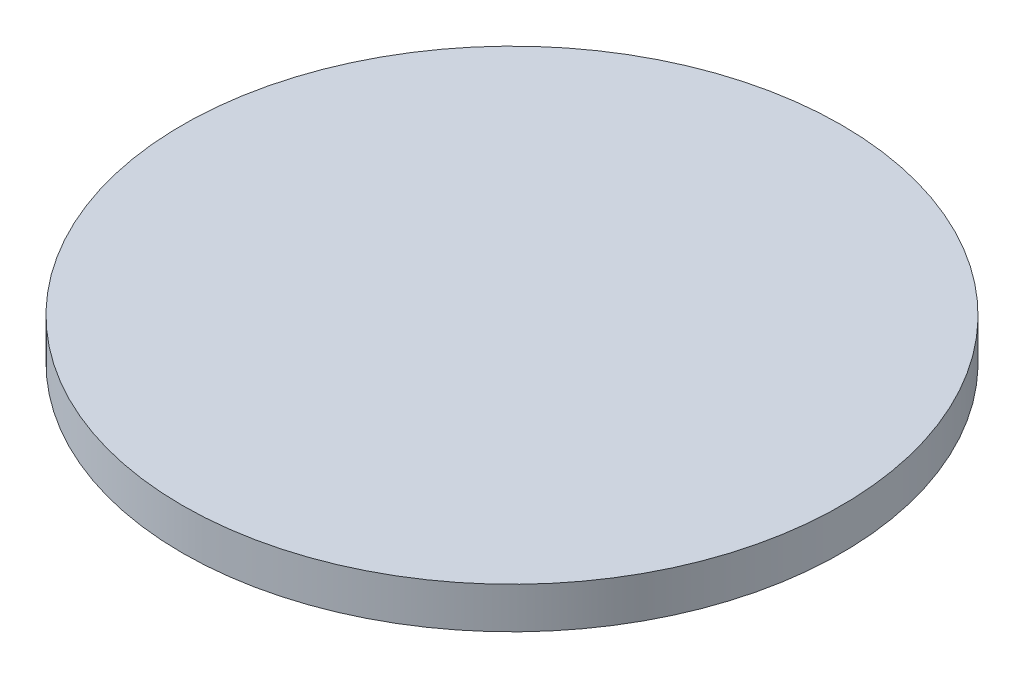
SolidWorks part; units mm, degrees
ref_plane "Front Plane" through (0, 0, 0) normal (0, 0, 1) x (1, 0, 0)
ref_plane "Top Plane" through (0, 0, 0) normal (0, 1, 0) x (1, 0, 0)
ref_plane "Right Plane" through (0, 0, 0) normal (1, 0, 0) x (0, 0, -1)
sketch "Sketch1" plane through (0, 0, 0) normal (0, 1, 0) x (1, 0, 0)
  circle A0 centre (0, 0) radius 152.4
extrude "Boss-Extrude1" add sketch "Sketch1" along normal blind 19.05
